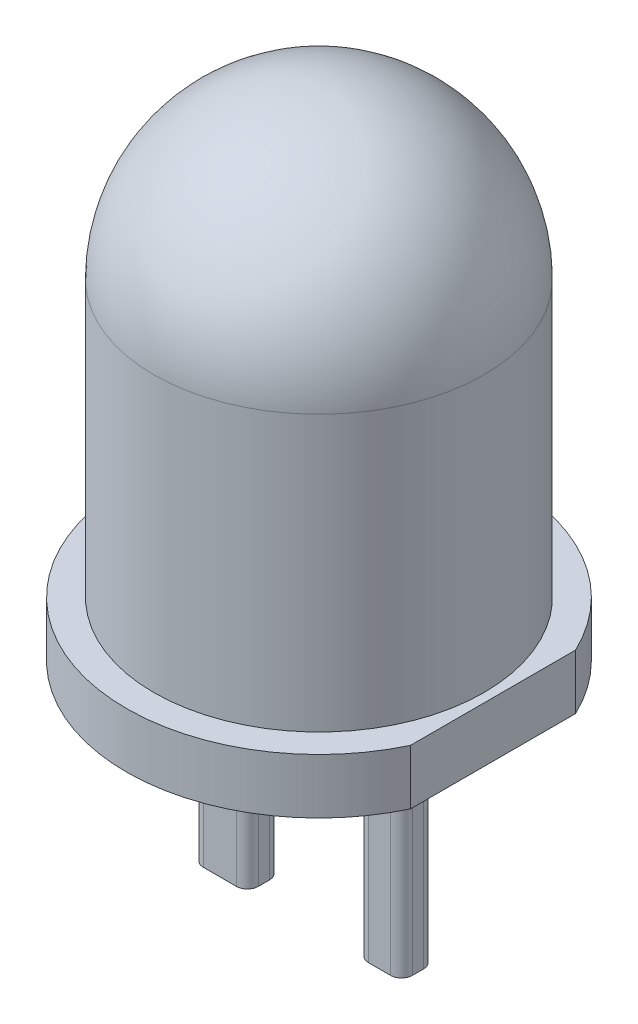
SolidWorks part; units mm, degrees
ref_plane "Ebene vorne" through (0, 0, 0) normal (0, 0, 1) x (1, 0, 0)
ref_plane "Ebene oben" through (0, 0, 0) normal (0, 1, 0) x (1, 0, 0)
ref_plane "Ebene rechts" through (0, 0, 0) normal (1, 0, 0) x (0, 0, -1)
sketch "Skizze2" plane through (0, 0, 0) normal (0, 0, 1) x (1, 0, 0)
  line L0 (0, 0) -> (0, 73.4838) construction
  line L1 (0, 0) -> (-1.75, 0)
  line L2 (-1.75, 0) -> (-1.75, 0.5)
  line L3 (-1.75, 0.5) -> (-1.5, 0.5)
  line L4 (-1.5, 0.5) -> (-1.5, 3)
  line L5 (0, 4.5) -> (0, 0)
  arc A0 (-1.5, 3) -> (0, 4.5) centre (0, 3) cw
  dimension "D1" = 4.5
  dimension "D2" = 0.5
  dimension "D3" = 1.75
  dimension "D4" = 2.5
  dimension "D5" = 1.5
revolve "Rotation1" add sketch "Skizze2" angle 360 about L0
sketch "Skizze3" plane through (0, 0, 0) normal (0, -1, 0) x (1, 0, 0)
  line L0 (1.5811, -0.75) -> (1.5811, 0.75)
  line L1 (0, 0) -> (1.75, 0) construction
  circle A0 centre (0, 0) radius 1.75 construction
  arc A1 (1.5811, -0.75) -> (1.5811, 0.75) centre (0, 0) ccw
  dimension "D1" = 1.5
extrude "Schnitt-Linear austragen1" cut sketch "Skizze3" against normal blind 1
sketch "Skizze4" plane through (0, 0, 0) normal (0, -1, 0) x (1, 0, 0)
  line L0 (-1.75, 0) -> (1.5811, 0) construction
  line L1 (0, 0) -> (0, 1.75) construction
  line L3 (1.5811, 0.75) -> (1.5811, -0.75) construction
  line L4 (0.6, 0.15) -> (0.8, 0.15)
  line L5 (0.5, 0.05) -> (0.5, -0.05)
  line L6 (0.6, -0.15) -> (0.8, -0.15)
  line L7 (0.9, 0.05) -> (0.9, -0.05)
  line L8 (-0.9, 0.15) -> (-0.6, 0.15)
  line L9 (-1, 0.05) -> (-1, -0.05)
  line L10 (-0.9, -0.15) -> (-0.6, -0.15)
  line L11 (-0.5, 0.05) -> (-0.5, -0.05)
  arc A0 (1.5811, 0.75) -> (1.5811, -0.75) centre (0, 0) ccw construction
  arc A1 (1.5811, 0.75) -> (1.5811, -0.75) centre (0, 0) ccw construction
  arc A2 (0.8, 0.15) -> (0.9, 0.05) centre (0.8, 0.05) cw
  arc A3 (0.6, 0.15) -> (0.5, 0.05) centre (0.6, 0.05) ccw
  arc A4 (0.5, -0.05) -> (0.6, -0.15) centre (0.6, -0.05) ccw
  arc A5 (0.8, -0.15) -> (0.9, -0.05) centre (0.8, -0.05) ccw
  arc A6 (-0.6, -0.15) -> (-0.5, -0.05) centre (-0.6, -0.05) ccw
  arc A7 (-0.6, 0.15) -> (-0.5, 0.05) centre (-0.6, 0.05) cw
  arc A8 (-0.9, 0.15) -> (-1, 0.05) centre (-0.9, 0.05) ccw
  arc A9 (-1, -0.05) -> (-0.9, -0.15) centre (-0.9, -0.05) ccw
  point P24 (0.9, 0.15)
  point P29 (0.5, -0.15)
  point P32 (0.9, -0.15)
  point P35 (-0.5, -0.15)
  point P40 (-1, 0.15)
  point P43 (-1, -0.15)
  dimension "D7" = 0.1
  dimension "D1" = 0.3
  dimension "D2" = 0.4
  dimension "D3" = 0.3
  dimension "D4" = 0.5
  dimension "D5" = 0.5
  dimension "D6" = 0.5
extrude "Linear austragen1" add sketch "Skizze4" along normal blind 2
